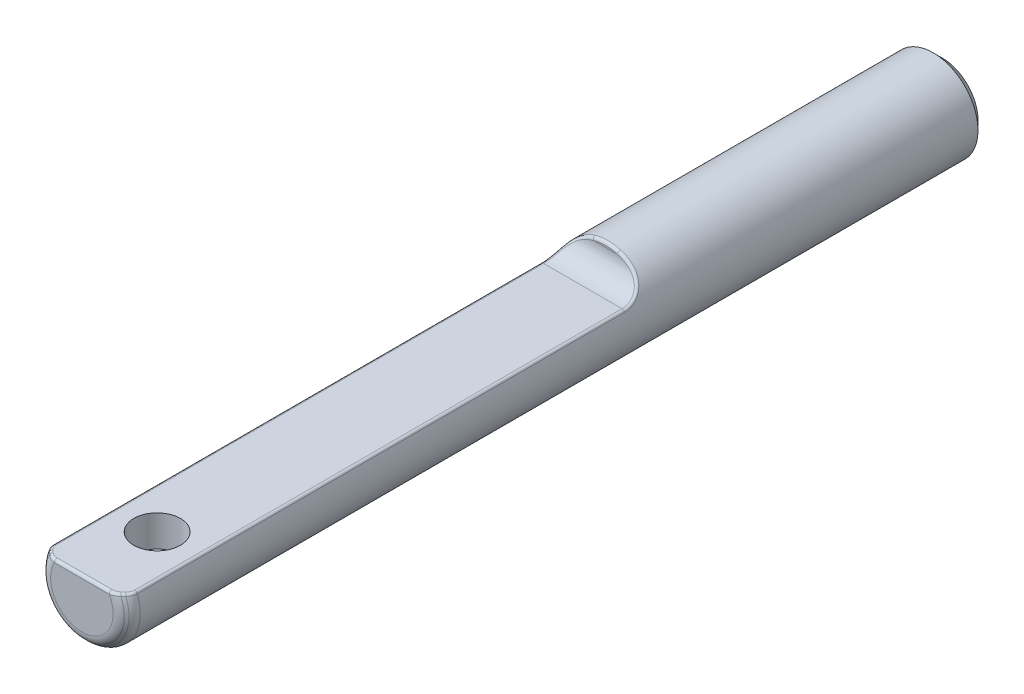
SolidWorks part; units mm, degrees
material "Alloy Steel"
ref_plane "Front" through (0, 0, 0) normal (0, 0, 1) x (1, 0, 0)
ref_plane "Top" through (0, 0, 0) normal (0, 1, 0) x (1, 0, 0)
ref_plane "Right" through (0, 0, 0) normal (1, 0, 0) x (0, 0, -1)
sketch "Sketch1" plane through (0, 0, 0) normal (0, 0, 1) x (1, 0, 0)
  circle A0 centre (0, 0) radius 3.175
  dimension "D1" = 6.35
extrude "Extrude1" add sketch "Sketch1" along normal mid plane 60.96
chamfer "Chamfer1" distance 0.635 angle 45 2 edges at (3.175, 0, -30.48) (3.175, 0, 30.48)
ref_plane "Plane1" through (0, 0, -6.604) normal (0, 0, 1) x (1, 0, 0)
sketch "Sketch13" plane through (0, 0, -6.604) normal (0, 0, 1) x (1, 0, 0)
  line L3 (-2.9099, 1.27) -> (2.9099, 1.27)
  circle A0 centre (0, 0) radius 3.175 construction
  arc A1 (2.9099, 1.27) -> (-2.9099, 1.27) centre (0, 0) ccw
  dimension "D1" = 1.27
extrude "Extrude7" cut sketch "Sketch13" along normal through all
fillet "Fillet1" radius 1.5875 1 edges at (0, 1.27, -6.604)
fillet "Fillet3" radius 0.7937 2 edges at (0, -2.54, 30.48) (0, -3.175, 29.845)
fillet "Fillet4" radius 0.1984 12 edges at (0, 1.27, 30.48) (2.207, 1.27, 30.4058) (-2.2045, 1.27, 30.4068) (2.8166, 1.27, 29.8742) (-2.8675, 1.27, 29.7615) (2.9099, 1.27, 12.2499) (-2.9099, 1.27, 12.2499) (-2.575, 1.8575, -6.2494) (2.7356, 1.6116, -6.0003) (0, 3.175, -6.604)
sketch "Sketch14" plane through (0, 1.27, 0) normal (0, 1, 0) x (1, 0, 0)
  line L0 (1.9342, -30.48) -> (-1.9342, -30.48) construction
  line L2 (-3.175, 29.845) -> (-3.175, -29.5162) construction
  circle A0 centre (0.0018, -25.146) radius 1.651
  dimension "D1" = 3.302
  dimension "D3" = 3.1768
  dimension "D2" = 5.334
extrude "Cut-Extrude1" cut sketch "Sketch14" against normal blind 2.2225
sketch3d "3DSketch1"
  line L0 (0, 0, -30.48) -> (0, 0, 30.48) construction
  line L2 (0, 0, -29.845) -> (0, 0, -30.48) construction
  line L3 (0, 0, 28.9998) -> (0, 0, 33.0916) construction
equation "\"D1@Chamfer1\" = \"D1@Sketch1\" * .1"
